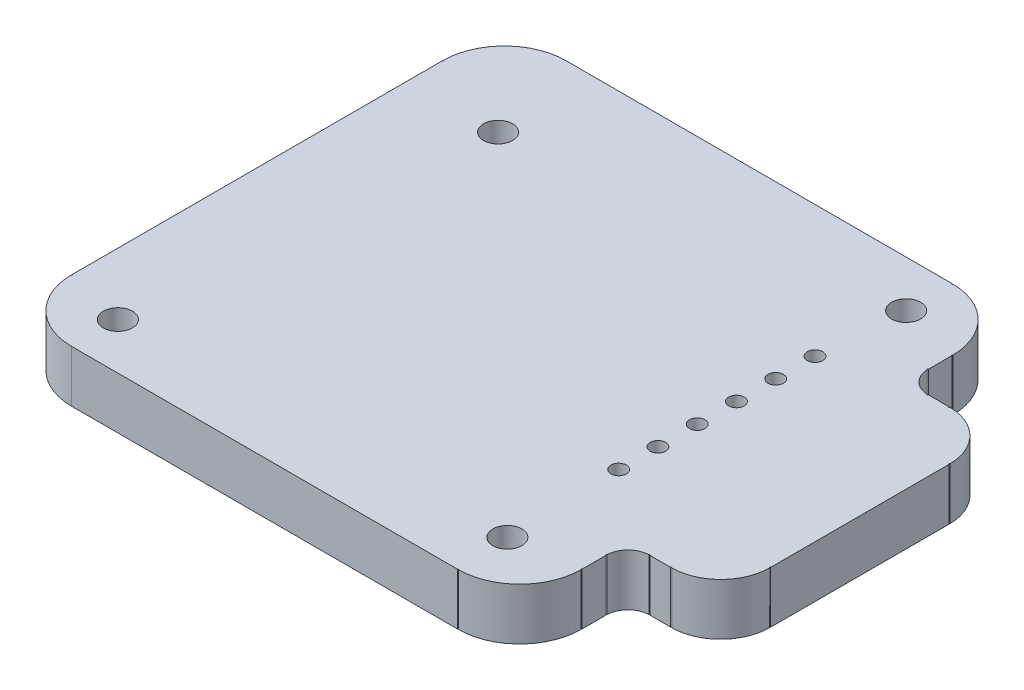
SolidWorks part; units mm, degrees
ref_plane "Front Plane" through (0, 0, 0) normal (0, 0, 1) x (1, 0, 0)
ref_plane "Top Plane" through (0, 0, 0) normal (0, 1, 0) x (1, 0, 0)
ref_plane "Right Plane" through (0, 0, 0) normal (1, 0, 0) x (0, 0, -1)
sketch "Sketch1" plane through (0, 0, 0) normal (0, 1, 0) x (1, 0, 0)
  line L0 (72.4533, 51.5868) -> (73.1533, 51.5868)
  line L1 (74.7533, 49.9868) -> (74.7533, 44.1868)
  line L2 (73.1533, 42.5868) -> (72.4533, 42.5868)
  line L3 (71.7533, 41.8868) -> (71.7533, 41.0868)
  line L4 (69.7533, 39.0868) -> (57.2533, 39.0868)
  line L5 (55.2533, 41.0868) -> (55.2533, 53.0868)
  line L6 (71.7533, 53.0868) -> (71.7533, 52.2868)
  line L7 (57.2533, 55.0868) -> (69.7533, 55.0868)
  arc A0 (73.1533, 51.5677) -> (73.1533, 51.6059) centre (73.1533, 51.5868) ccw
  arc A1 (72.4533, 51.6059) -> (72.4533, 51.5677) centre (72.4533, 51.5868) ccw
  arc A2 (74.7342, 44.1868) -> (74.7724, 44.1868) centre (74.7533, 44.1868) ccw
  arc A3 (74.7724, 49.9868) -> (74.7342, 49.9868) centre (74.7533, 49.9868) ccw
  arc A4 (72.4533, 42.6059) -> (72.4533, 42.5677) centre (72.4533, 42.5868) ccw
  arc A5 (73.1533, 42.5677) -> (73.1533, 42.6059) centre (73.1533, 42.5868) ccw
  arc A6 (71.7342, 41.0868) -> (71.7724, 41.0868) centre (71.7533, 41.0868) ccw
  arc A7 (71.7724, 41.8868) -> (71.7342, 41.8868) centre (71.7533, 41.8868) ccw
  arc A8 (69.7533, 39.0677) -> (69.7533, 39.1059) centre (69.7533, 39.0868) ccw
  arc A9 (55.2724, 53.0868) -> (55.2342, 53.0868) centre (55.2533, 53.0868) ccw
  arc A10 (55.2342, 41.0868) -> (55.2724, 41.0868) centre (55.2533, 41.0868) ccw
  arc A11 (71.7342, 52.2868) -> (71.7724, 52.2868) centre (71.7533, 52.2868) ccw
  arc A12 (71.7724, 53.0868) -> (71.7342, 53.0868) centre (71.7533, 53.0868) ccw
  arc A13 (69.7533, 55.0677) -> (69.7533, 55.1059) centre (69.7533, 55.0868) ccw
  arc A14 (71.7533, 52.2868) -> (72.4533, 51.5868) centre (72.4533, 52.2868) ccw
  arc A15 (71.7724, 52.2868) -> (71.7342, 52.2868) centre (71.7533, 52.2868) ccw
  arc A16 (72.4533, 51.5677) -> (72.4533, 51.6059) centre (72.4533, 51.5868) ccw
  arc A17 (72.4533, 42.5868) -> (71.7533, 41.8868) centre (72.4533, 41.8868) ccw
  arc A18 (72.4533, 42.5677) -> (72.4533, 42.6059) centre (72.4533, 42.5868) ccw
  arc A19 (71.7342, 41.8868) -> (71.7724, 41.8868) centre (71.7533, 41.8868) ccw
  arc A20 (57.2533, 55.0868) -> (55.2533, 53.0868) centre (57.2534, 53.0867) ccw
  arc A21 (55.2342, 53.0868) -> (55.2724, 53.0868) centre (55.2533, 53.0868) ccw
  arc A22 (71.7533, 53.0868) -> (69.7533, 55.0868) centre (69.7532, 53.0867) ccw
  arc A23 (71.7342, 53.0868) -> (71.7724, 53.0868) centre (71.7533, 53.0868) ccw
  arc A24 (69.7533, 55.1059) -> (69.7533, 55.0677) centre (69.7533, 55.0868) ccw
  arc A25 (69.7533, 39.0868) -> (71.7533, 41.0868) centre (69.7532, 41.0869) ccw
  arc A26 (69.7533, 39.1059) -> (69.7533, 39.0677) centre (69.7533, 39.0868) ccw
  arc A27 (71.7724, 41.0868) -> (71.7342, 41.0868) centre (71.7533, 41.0868) ccw
  arc A28 (55.2533, 41.0868) -> (57.2533, 39.0868) centre (57.2534, 41.0869) ccw
  arc A29 (55.2724, 41.0868) -> (55.2342, 41.0868) centre (55.2533, 41.0868) ccw
  arc A30 (74.7533, 49.9868) -> (73.1533, 51.5868) centre (73.1533, 49.9867) ccw
  arc A31 (74.7342, 49.9868) -> (74.7724, 49.9868) centre (74.7533, 49.9868) ccw
  arc A32 (73.1533, 51.6059) -> (73.1533, 51.5677) centre (73.1533, 51.5868) ccw
  arc A33 (73.1533, 42.5868) -> (74.7533, 44.1868) centre (73.1533, 44.1868) ccw
  arc A34 (73.1533, 42.6059) -> (73.1533, 42.5677) centre (73.1533, 42.5868) ccw
  arc A35 (74.7724, 44.1868) -> (74.7342, 44.1868) centre (74.7533, 44.1868) ccw
  arc A36 (74.7533, 51.6193) -> (74.7533, 51.5543) centre (74.7533, 51.5868) ccw
  circle A37 centre (57.2533, 40.5868) radius 0.4699
  circle A38 centre (57.2533, 40.5868) radius 0.4699
  circle A39 centre (58.1533, 51.9868) radius 0.4699
  circle A40 centre (58.1533, 51.9868) radius 0.4699
  circle A41 centre (69.5533, 44.4868) radius 0.25
  circle A42 centre (69.5533, 44.4868) radius 0.25
  circle A43 centre (69.5533, 45.7568) radius 0.25
  circle A44 centre (69.5533, 45.7568) radius 0.25
  circle A45 centre (69.5533, 47.0268) radius 0.25
  circle A46 centre (69.5533, 47.0268) radius 0.25
  circle A47 centre (69.5533, 48.2968) radius 0.25
  circle A48 centre (69.5533, 48.2968) radius 0.25
  circle A49 centre (69.5533, 49.5668) radius 0.25
  circle A50 centre (69.5533, 49.5668) radius 0.25
  circle A51 centre (69.5533, 50.8368) radius 0.25
  circle A52 centre (69.5533, 50.8368) radius 0.25
  circle A53 centre (69.7533, 53.5868) radius 0.4699
  circle A54 centre (69.7533, 53.5868) radius 0.4699
  circle A55 centre (69.6533, 40.7868) radius 0.4699
  circle A56 centre (69.6533, 40.7868) radius 0.4699
extrude "Boss-Extrude1" add sketch "Sketch1" along normal blind 1.6764 contours A35 L1 A31 A3 A30 A0 A32 L0 A16 A1 A14 A11 A15 L6 A23 A12 A22 A13 A24 L7 A20 A9 A21 L5 A29 A10 A28 L4 A26 A8 A25 A6 A27 L3 A19 A7 A17 A4 A18 L2 A34 A5 A33 A2 A55 A53 A51
